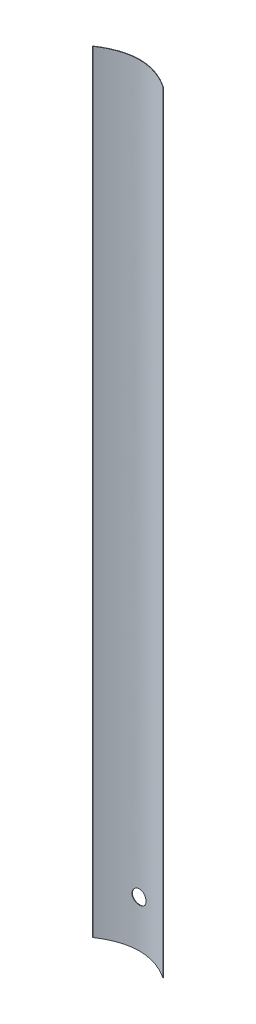
SolidWorks part; units mm, degrees
ref_plane "Front Plane" through (0, 0, 0) normal (0, 0, 1) x (1, 0, 0)
ref_plane "Top Plane" through (0, 0, 0) normal (0, 1, 0) x (1, 0, 0)
ref_plane "Right Plane" through (0, 0, 0) normal (1, 0, 0) x (0, 0, -1)
sketch "Sketch1" plane through (0, 0, 0) normal (0, 1, 0) x (1, 0, 0)
  line L0 (7.55, -2.55) -> (7.45, -2.55)
  line L1 (-7.45, -2.55) -> (-7.55, -2.55)
  spline S0 degree 2 poles (7.55, -2.55) (0, 2.55) (-7.55, -2.55) knots 0 0 0 1 1 1
  spline S1 degree 2 poles (-7.45, -2.55) (0, 2.35) (7.45, -2.55) knots 0 0 0 1 1 1
  point P6 (0, 0)
  dimension "D1" = 2.45
  dimension "D2" = 2.55
  dimension "D3" = 0.1
  dimension "D4" = 7.45
  dimension "D5" = 7.45
  dimension "D6" = 7.55
extrude "Boss-Extrude1" add sketch "Sketch1" along normal blind 165.1
sketch "Sketch2" plane through (0, 0, 0) normal (0, 0, 1) x (1, 0, 0)
  circle A0 centre (0, 10) radius 1.5
  point P2 (0, 0)
  dimension "D1" = 3
  dimension "D2" = 10
extrude "Cut-Extrude1" cut sketch "Sketch2" along normal through all
